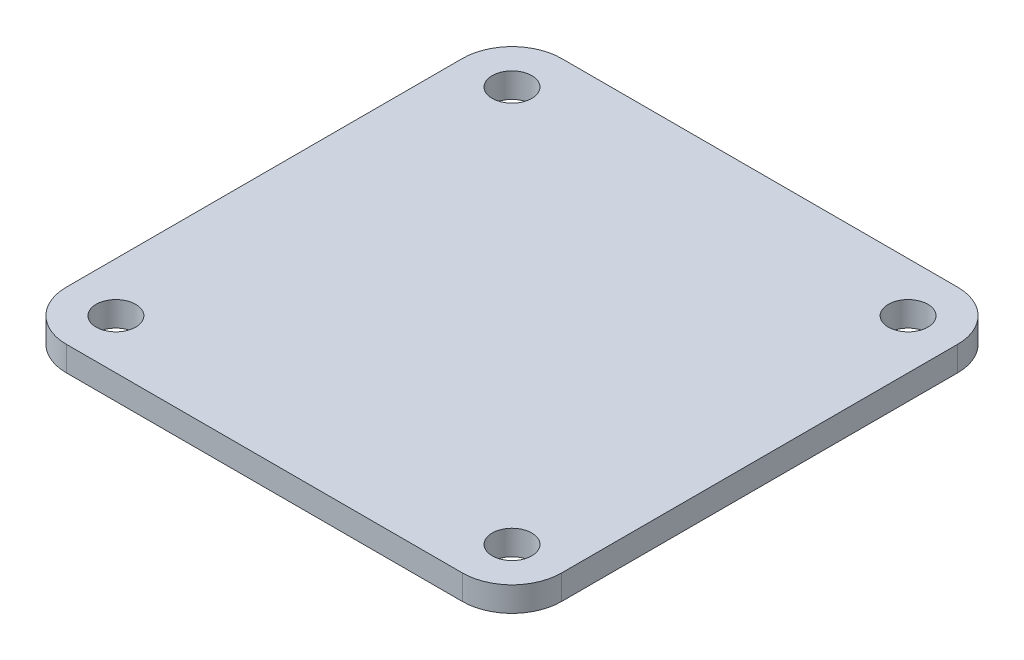
SolidWorks part; units mm, degrees
material "AISI 1020 Steel, Cold Rolled"
ref_plane "Front Plane" through (0, 0, 0) normal (0, 0, 1) x (1, 0, 0)
ref_plane "Top Plane" through (0, 0, 0) normal (0, 1, 0) x (1, 0, 0)
ref_plane "Right Plane" through (0, 0, 0) normal (1, 0, 0) x (0, 0, -1)
sketch "Sketch1" plane through (0, 0, 0) normal (0, 1, 0) x (1, 0, 0)
  line L1 (50, -50) -> (-50, -50)
  line L2 (50, -50) -> (50, 50)
  line L3 (50, 50) -> (-50, 50)
  line L4 (-50, -50) -> (-50, 50)
  line L5 (50, -50) -> (-50, 50) construction
  line L6 (50, 50) -> (-50, -50) construction
  point P0 (0, 0)
  dimension "D1" = 100
  dimension "D2" = 100
extrude "Boss-Extrude1" add sketch "Sketch1" along normal blind 5
hole_wizard "Ø8.0mm Dowel Hole1" positions "Sketch12" profile "Sketch13" hole size "Ø8.0" standard "ISO" end condition up to next
sketch "Sketch12" plane through (0, 5, 0) normal (0, 1, 0) x (1, 0, 0)
  line L0 (50, 50) -> (-50, 50) construction
  line L1 (-50, 50) -> (-50, -50) construction
  point P0 (-40, -40)
  point P2 (-40, 40)
  point P4 (40, 40)
  point P6 (40, -40)
  dimension "D1" = 80
  dimension "D2" = 80
  dimension "D3" = 10
  dimension "D4" = 10
sketch "Sketch13" plane through (-40, 5, 40) normal (1, 0, 0) x (0, 0, 1)
  line L0 (0, 0) -> (0, 5)
  line L1 (0, 5) -> (4, 5)
  line L2 (4, 5) -> (4, 0)
  line L5 (4, 0) -> (0, 0)
  line L11 (0, -6.35) -> (0, 107.95) construction
  dimension "Thru Hole Dia." = 8
  dimension "Thru Hole Depth" = 5
fillet "Fillet1" radius 10 4 edges at (50, 2.5, -50) (50, 2.5, 50) (-50, 2.5, 50) (-50, 2.5, -50)
